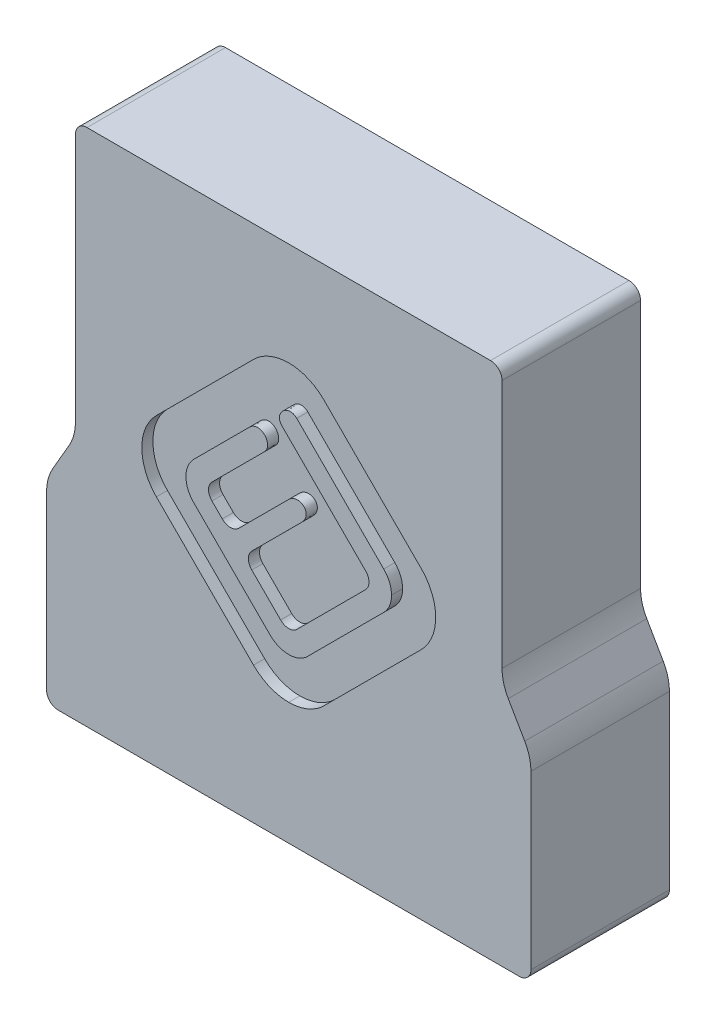
SolidWorks part; units mm, degrees
material "Mahogany"
ref_plane "Front Plane" through (0, 0, 0) normal (0, 0, 1) x (1, 0, 0)
ref_plane "Top Plane" through (0, 0, 0) normal (0, 1, 0) x (1, 0, 0)
ref_plane "Right Plane" through (0, 0, 0) normal (1, 0, 0) x (0, 0, -1)
sketch "Sketch1" plane through (0, 0, 0) normal (0, 0, 1) x (1, 0, 0)
  line L0 (-17.4943, -33.274) -> (17.4943, -33.274)
  line L1 (17.4943, -33.274) -> (17.4943, -38.862)
  line L2 (17.4943, -38.862) -> (30.1308, -38.862)
  line L3 (30.1308, -38.862) -> (30.1308, -18.288)
  line L4 (30.1308, -18.288) -> (26.162, -18.288)
  line L5 (26.162, 26.162) -> (-26.162, 26.162)
  line L6 (0, 0) -> (0, -33.274) construction
  line L7 (26.162, -18.288) -> (26.162, 26.162)
  line L15 (-26.162, -18.288) -> (-26.162, 26.162)
  line L16 (-30.1308, -18.288) -> (-26.162, -18.288)
  line L17 (-30.1308, -38.862) -> (-30.1308, -18.288)
  line L18 (-17.4943, -38.862) -> (-30.1308, -38.862)
  line L19 (-17.4943, -33.274) -> (-17.4943, -38.862)
  point P26 (0, 26.162)
  dimension "D1" = 59.436
  dimension "D2" = 34.9885
  dimension "D3" = 65.024
  dimension "D4" = 60.2615
  dimension "D5" = 20.574
  dimension "D6" = 52.324
  dimension "D7" = 26.162
extrude "Overlap Profile" add sketch "Sketch1" against normal blind 5.08 thin
sketch "Sketch2" plane through (0, 0, 0) normal (0, 0, 1) x (1, 0, 0)
  line L0 (-29.337, 29.337) -> (-29.337, -15.113) construction
  line L1 (29.337, 29.337) -> (-29.337, 29.337) construction
  line L2 (29.337, -15.113) -> (29.337, 29.337) construction
  line L3 (33.3058, -15.113) -> (29.337, -15.113) construction
  line L4 (33.3058, -42.037) -> (33.3058, -15.113) construction
  line L5 (14.3193, -42.037) -> (33.3058, -42.037) construction
  line L6 (14.3193, -36.449) -> (14.3193, -42.037) construction
  line L7 (-14.3193, -36.449) -> (14.3193, -36.449) construction
  line L8 (-14.3193, -42.037) -> (-14.3193, -36.449) construction
  line L9 (-33.3058, -42.037) -> (-14.3193, -42.037) construction
  line L10 (-33.3058, -15.113) -> (-33.3058, -42.037) construction
  line L11 (-29.337, -15.113) -> (-33.3058, -15.113) construction
  line L12 (-29.337, 29.337) -> (-29.337, -15.113)
  line L13 (29.337, 29.337) -> (-29.337, 29.337)
  line L14 (29.337, -15.113) -> (29.337, 29.337)
  line L15 (33.3058, -15.113) -> (29.337, -15.113)
  line L16 (33.3058, -42.037) -> (33.3058, -15.113)
  line L17 (14.3193, -42.037) -> (33.3058, -42.037)
  line L18 (14.3193, -36.449) -> (14.3193, -42.037)
  line L19 (-14.3193, -36.449) -> (14.3193, -36.449)
  line L20 (-14.3193, -42.037) -> (-14.3193, -36.449)
  line L21 (-33.3058, -42.037) -> (-14.3193, -42.037)
  line L22 (-33.3058, -15.113) -> (-33.3058, -42.037)
  line L23 (-29.337, -15.113) -> (-33.3058, -15.113)
extrude "End Thickness" add sketch "Sketch2" along normal blind 13.97
fillet "Fillet1" radius 1.5875 12 edges at (-26.162, 26.162, -2.54) (-26.162, -18.288, -2.54) (-30.1308, -18.288, -2.54) (-30.1308, -38.862, -2.54) (17.4943, -33.274, -2.54) (17.4943, -38.862, -2.54) (30.1308, -38.862, -2.54) (30.1308, -18.288, -2.54) (26.162, -18.288, -2.54) (26.162, 26.162, -2.54) (-17.4943, -33.274, -2.54) (-17.4943, -38.862, -2.54)
fillet "Fillet2" radius 1.5875 4 edges at (-29.337, 29.337, 4.445) (29.337, 29.337, 4.445) (33.3058, -42.037, 4.445) (-33.3058, -42.037, 4.445)
sketch "Sketch7" plane through (0, 0, -5.08) normal (0, 0, -1) x (-1, 0, 0)
  line L1 (-14.3193, -36.449) -> (14.3193, -36.449)
  line L2 (-14.3193, -36.449) -> (-14.3193, -42.037)
  line L3 (-14.3193, -42.037) -> (14.3193, -42.037)
  line L4 (14.3193, -36.449) -> (14.3193, -42.037)
extrude "Bottom Fill" add sketch "Sketch7" against normal up to surface (19.05 mm away) up to face at (0, -16.764, 13.97)
sketch "Sketch5" plane through (0, 0, 13.97) normal (0, 0, 1) x (1, 0, 0)
  line L0 (13.0646, -8.006) -> (2.5845, -18.4871)
  line L1 (-2.5844, -18.4855) -> (-13.0646, -8.006)
  line L2 (-11.085, -6.0269) -> (-8.0174, -9.0969)
  line L3 (-6.2094, -10.9033) -> (-0.6055, -16.5074)
  line L4 (0.606, -16.5078) -> (11.0865, -6.0272)
  line L5 (18.2052, -0.1879) -> (4.8438, 13.1736)
  line L6 (-4.8432, 13.1736) -> (-18.2053, -0.1879)
  line L7 (-18.2049, -9.8749) -> (-4.8432, -23.2365)
  line L8 (4.8438, -23.2365) -> (18.2052, -9.8749)
  line L9 (0, 13.9458) -> (0, 70.9204) construction
  spline S0 degree 3 poles (2.5845, -18.4871) (1.8952, -19.1776) (0.9773, -19.5586) (0, -19.5575) knots 1 1 1 1 2 2 2 2
  spline S1 degree 3 poles (0, -19.5575) (-0.9767, -19.5575) (-1.8933, -19.1776) (-2.5844, -18.4855) knots 2 2 2 2 3 3 3 3
  spline S2 degree 3 poles (-13.0646, -8.006) (-13.756, -7.316) (-14.136, -6.3986) (-14.136, -5.4217) knots 4 4 4 4 5 5 5 5
  spline S3 degree 3 poles (-14.136, -5.4217) (-14.136, -4.4447) (-13.7556, -3.5278) (-13.0646, -2.8373) knots 5 5 5 5 6 6 6 6
  spline S4 degree 2 poles (-13.0646, -2.8373) (-8.1998, 2.0277) (-5.4287, 4.7988) knots 6 6 6 7 7 7
  spline S5 degree 3 poles (-5.4287, 4.7988) (-3.8393, 6.3872) (-2.073, 4.196) (-3.3333, 2.9364) knots 7 7 7 7 8 8 8 8
  spline S6 degree 2 poles (-3.3333, 2.9364) (-6.1042, 0.1638) (-11.0861, -4.8163) knots 8 8 8 9 9 9
  spline S7 degree 3 poles (-11.0861, -4.8163) (-11.2473, -4.9784) (-11.3367, -5.1929) (-11.3367, -5.4217) knots 9 9 9 9 10 10 10 10
  spline S8 degree 3 poles (-11.3367, -5.4217) (-11.3361, -5.6501) (-11.2473, -5.8652) (-11.085, -6.0269) knots 10 10 10 10 11 11 11 11
  spline S9 degree 2 poles (-8.0174, -9.0969) (-1.828, -2.9089) (-0.0253, -1.1061) knots 12 12 12 13 13 13
  spline S10 degree 3 poles (-0.0253, -1.1061) (1.429, 0.3476) (3.4298, -1.2637) (1.8008, -2.8935) knots 13 13 13 13 14 14 14 14
  spline S11 degree 2 poles (1.8008, -2.8935) (0.0954, -4.5994) (-6.2094, -10.9033) knots 14 14 14 15 15 15
  spline S12 degree 3 poles (-0.6055, -16.5074) (-0.4437, -16.6691) (-0.2284, -16.7584) (0, -16.7584) knots 16 16 16 16 17 17 17 17
  spline S13 degree 3 poles (0, -16.7584) (0.2296, -16.7584) (0.4438, -16.6698) (0.606, -16.5078) knots 17 17 17 17 18 18 18 18
  spline S14 degree 3 poles (11.0865, -6.0272) (11.2476, -5.8652) (11.3364, -5.6494) (11.3368, -5.4226) knots 19 19 19 19 20 20 20 20
  spline S15 degree 3 poles (11.3368, -5.4226) (11.3368, -5.1929) (11.2476, -4.9777) (11.0858, -4.8163) knots 20 20 20 20 21 21 21 21
  spline S16 degree 2 poles (11.0858, -4.8163) (2.5929, 3.6758) (-0.914, 7.1841) knots 21 21 21 22 22 22
  spline S17 degree 3 poles (-0.914, 7.1841) (-2.1169, 8.3858) (-0.0785, 10.3075) (1.1034, 9.1246) knots 22 22 22 22 23 23 23 23
  spline S18 degree 2 poles (1.1034, 9.1246) (4.6697, 5.5578) (13.0646, -2.8373) knots 23 23 23 24 24 24
  spline S19 degree 3 poles (13.0646, -2.8373) (13.7564, -3.5274) (14.1361, -4.4447) (14.1361, -5.4213) knots 24 24 24 24 25 25 25 25
  spline S20 degree 3 poles (14.1361, -5.4213) (14.1361, -6.3974) (13.7564, -7.316) (13.0646, -8.006) knots 25 25 25 25 26 26 26 26
  spline S21 degree 3 poles (4.8438, 13.1736) (3.5495, 14.4676) (1.8293, 15.1801) (0, 15.1801) knots 1 1 1 1 2 2 2 2
  spline S22 degree 3 poles (0, 15.1801) (-1.8295, 15.1801) (-3.5499, 14.4676) (-4.8432, 13.1736) knots 2 2 2 2 3 3 3 3
  spline S23 degree 3 poles (-18.2053, -0.1879) (-20.8754, -2.8587) (-20.8754, -7.204) (-18.2049, -9.8749) knots 4 4 4 4 5 5 5 5
  spline S24 degree 3 poles (-4.8432, -23.2365) (-3.5499, -24.5303) (-1.8295, -25.2429) (0, -25.2429) knots 6 6 6 6 7 7 7 7
  spline S25 degree 3 poles (0, -25.2429) (1.8293, -25.2429) (3.5495, -24.5303) (4.8438, -23.2365) knots 7 7 7 7 8 8 8 8
  spline S26 degree 3 poles (18.2052, -9.8749) (20.8765, -7.204) (20.8765, -2.8587) (18.2052, -0.1879) knots 9 9 9 9 10 10 10 10
extrude "Logo Inlay Cutout" cut sketch "Sketch5" against normal blind 1.524
sketch "Sketch9" plane through (0, 0, 13.97) normal (0, 0, 1) x (1, 0, 0)
  line L0 (-33.3058, -15.113) -> (-29.337, -8.2389)
  line L1 (-29.337, 27.7495) -> (-29.337, -15.113) construction
  line L2 (-29.337, -8.2389) -> (-29.337, -15.113)
  line L3 (-29.337, -15.113) -> (-33.3058, -15.113)
  line L4 (0, 0) -> (0, -49.9352) construction
  line L5 (29.337, -15.113) -> (33.3058, -15.113)
  line L6 (29.337, -8.2389) -> (29.337, -15.113)
  line L7 (33.3058, -15.113) -> (29.337, -8.2389)
  dimension "D1" = 60
extrude "Side Transition Fill" add sketch "Sketch9" against normal up to surface (19.05 mm away)
sketch "Sketch8" plane through (0, 0, 0) normal (0, 0, -1) x (-1, 0, 0)
  line L0 (-26.162, -16.7005) -> (-26.162, 24.5745) construction
  line L1 (-26.162, -2.0955) -> (26.162, -2.0955)
  line L2 (-26.162, -2.0955) -> (-26.162, -22.9235)
  line L3 (-26.162, -22.9235) -> (26.162, -22.9235)
  line L4 (26.162, -2.0955) -> (26.162, -22.9235)
  line L5 (26.162, 24.5745) -> (26.162, -16.7005) construction
  line L8 (31.7183, -42.037) -> (-31.7183, -42.037) construction
  dimension "D1" = 19.1135
  dimension "D2" = 39.9415
extrude "Magnetic Catch Cutout" cut sketch "Sketch8" against normal blind 7.62
fillet "Fillet3" radius 6.35 2 edges at (29.337, -8.2389, 4.445) (-29.337, -8.2389, 4.445)
fillet "Fillet4" radius 6.35 2 edges at (33.3058, -15.113, 4.445) (-33.3058, -15.113, 4.445)
sketch "Sketch10" plane through (0, 0, 0) normal (0, 0, -1) x (-1, 0, 0)
  line L0 (26.162, -2.0955) -> (-26.162, -2.0955) construction
  line L1 (-26.162, -22.9235) -> (26.162, -22.9235) construction
  line L2 (-26.162, -16.7005) -> (-26.162, 24.5745) construction
  line L3 (-26.162, -2.0955) -> (-26.162, -22.9235) construction
  line L4 (26.162, -22.9235) -> (26.162, -16.7005) construction
  line L5 (26.162, 24.5745) -> (26.162, -2.0955) construction
  circle A0 centre (-22.987, -2.0955) radius 3.175
  circle A1 centre (-22.987, -22.9235) radius 3.175
  circle A2 centre (22.987, -22.9235) radius 3.175
  circle A3 centre (22.987, -2.0955) radius 3.175
  dimension "D1" = 6.35
extrude "Router Bit Relief" cut sketch "Sketch10" against normal up to surface (7.62 mm away) up to face at (0, -12.5095, 7.62)
fillet "Fillet5" radius 3.175 4 edges at (-19.812, -2.0955, 3.81) (-19.812, -22.9235, 3.81) (19.812, -22.9235, 3.81) (19.812, -2.0955, 3.81)
sketch "Sketch15" plane through (0, 0, 13.97) normal (0, 0, 1) x (1, 0, 0)
  line L0 (-8.0174, -9.0969) -> (-11.085, -6.0269) construction
  line L1 (-8.0174, -9.0969) -> (-11.085, -6.0269) construction
  line L2 (-0.6055, -16.5074) -> (-6.2094, -10.9033) construction
  line L3 (11.0865, -6.0272) -> (0.606, -16.5078) construction
  line L4 (11.0865, -6.0272) -> (0.606, -16.5078) construction
  line L5 (1.123, -15.9908) -> (0.606, -16.5078)
  line L6 (-5.0869, -12.0259) -> (-6.2094, -10.9033)
  line L7 (-10.5689, -6.5434) -> (-11.085, -6.0269)
  line L18 (2.5845, -18.4871) -> (13.0646, -8.006)
  line L19 (11.0865, -6.0272) -> (0.606, -16.5078)
  line L20 (-0.6055, -16.5074) -> (-6.2094, -10.9033)
  line L21 (-8.0174, -9.0969) -> (-11.085, -6.0269)
  line L22 (-13.0646, -8.006) -> (-2.5844, -18.4855)
  line L24 (11.0865, -6.0272) -> (10.569, -6.5446)
  line L25 (-0.6055, -16.5074) -> (-1.1221, -15.9908)
  line L26 (-8.0174, -9.0969) -> (-9.1398, -7.9736)
  arc A0 (-10.5682, -4.2986) -> (-10.5689, -6.5434) centre (-9.4459, -5.4213) ccw
  arc A1 (-9.1398, -7.9736) -> (-6.8944, -7.9742) centre (-8.0168, -6.8515) ccw
  arc A2 (-5.0868, -9.7808) -> (-5.0869, -12.0259) centre (-3.9643, -10.9034) ccw
  arc A3 (-1.1221, -15.9908) -> (1.123, -15.9908) centre (0.0004, -14.8683) ccw
  arc A4 (10.569, -6.5446) -> (10.569, -4.2995) centre (9.4465, -5.4221) ccw
  spline S0 degree 2 poles (-11.0861, -4.8163) (-6.1042, 0.1638) (-3.3333, 2.9364) knots 8 8 8 9 9 9 construction
  spline S2 degree 2 poles (-0.0253, -1.1061) (-1.828, -2.9089) (-8.0174, -9.0969) knots 12 12 12 13 13 13 construction
  spline S3 degree 2 poles (-6.2094, -10.9033) (0.0954, -4.5994) (1.8008, -2.8935) knots 14 14 14 15 15 15 construction
  spline S4 degree 2 poles (-0.914, 7.1841) (2.5929, 3.6758) (11.0858, -4.8163) knots 21 21 21 22 22 22 construction
  spline S38 degree 3 poles (39.3725, 991.6475) (-248.9242, -982.5134) (490.0971, 884.4746) (-651.7572, -751.4605) knots 8.019112 8.019112 8.019112 8.019112 43.041313 43.041313 43.041313 43.041313 only from (13.0646, -8.006) to (14.1361, -5.4213)
  spline S39 degree 3 poles (-658.7252, 734.3466) (496.1293, -891.1219) (-253.4308, 969.6155) (41.6749, -1002.414) knots 6.887684 6.887684 6.887684 6.887684 42.07325 42.07325 42.07325 42.07325 only from (14.1361, -5.4213) to (13.0646, -2.8373)
  spline S40 degree 2 poles (720.1797, -709.9348) (-717.2395, 727.4377) (708.2263, -697.9529) knots 12.5129 12.5129 12.5129 36.862628 36.862628 36.862628 only from (13.0646, -2.8373) to (1.1034, 9.1246)
  spline S41 degree 3 poles (-611.0838, -781.5838) (706.3628, 742.4374) (-781.2676, -645.7301) (829.654, 564.0856) knots 16.842586 16.842586 16.842586 16.842586 28.136888 28.136888 28.136888 28.136888 only from (1.1034, 9.1246) to (-0.914, 7.1841)
  spline S42 degree 2 poles (2120.8758, -2113.5966) (-2133.5368, 2138.9167) (2132.6918, -2125.6396) knots -0.344255 -0.344255 -0.344255 40.994874 40.994874 40.994874 only from (-0.914, 7.1841) to (11.0858, -4.8163)
  spline S43 degree 3 poles (749.7299, -2908.8051) (-1016.2633, 2816.4948) (1313.8777, -2710.6912) (-1552.3955, 2550.6403) knots -20.721468 -20.721468 -20.721468 -20.721468 61.722928 61.722928 61.722928 61.722928 only from (11.0858, -4.8163) to (11.3368, -5.4226)
  spline S44 degree 3 poles (-1427.7352, -2634.0556) (1198.8921, 2755.3096) (-912.4021, -2865.8999) (658.5281, 2920.0551) knots -20.883865 -20.883865 -20.883865 -20.883865 59.79428 59.79428 59.79428 59.79428 only from (11.3368, -5.4226) to (11.0865, -6.0272)
  spline S45 degree 3 poles (-2912.0245, -719.0392) (2827.1464, 989.0057) (-2706.3149, -1311.3968) (2552.1599, 1552.6637) knots -24.742629 -24.742629 -24.742629 -24.742629 59.741029 59.741029 59.741029 59.741029 only from (0.606, -16.5078) to (0, -16.7584)
  spline S46 degree 3 poles (-2566.651, 1529.8627) (2711.8644, -1308.3233) (-2825.0037, 1005.8401) (2903.3943, -755.939) knots -24.336799 -24.336799 -24.336799 -24.336799 57.358319 57.358319 57.358319 57.358319 only from (0, -16.7584) to (-0.6055, -16.5074)
  spline S47 degree 2 poles (-2127.7761, -2131.8916) (2128.631, 2123.3195) (-2119.761, -2123.7978) knots -6.150124 -6.150124 -6.150124 36.851174 36.851174 36.851174 only from (-6.2094, -10.9033) to (1.8008, -2.8935)
  spline S48 degree 3 poles (-912.4395, 402.2691) (857.2638, -534.4785) (-768.436, 649.0923) (660.6969, -751.7121) knots 7.784488 7.784488 7.784488 7.784488 19.343438 19.343438 19.343438 19.343438 only from (1.8008, -2.8935) to (-0.0253, -1.1061)
  spline S49 degree 2 poles (-2121.7285, -2122.0307) (2127.0994, 2125.2715) (-2129.6154, -2129.9796) knots -10.407218 -10.407218 -10.407218 33.626154 33.626154 33.626154 only from (-0.0253, -1.1061) to (-8.0174, -9.0969)
  spline S50 degree 3 poles (-604.873, 2931.0468) (873.0827, -2875.7574) (-1174.7296, 2762.9648) (1419.4807, -2638.2337) knots -30.649604 -30.649604 -30.649604 -30.649604 51.821766 51.821766 51.821766 51.821766 only from (-11.085, -6.0269) to (-11.3367, -5.4217)
  spline S51 degree 3 poles (1652.0366, 2487.0149) (-1419.3533, -2657.1876) (1125.0895, 2774.2857) (-859.2116, -2878.6067) knots -31.901781 -31.901781 -31.901781 -31.901781 51.089545 51.089545 51.089545 51.089545 only from (-11.3367, -5.4217) to (-11.0861, -4.8163)
  spline S52 degree 2 poles (-2133.9266, -2124.5614) (2130.5056, 2133.3187) (-2126.5341, -2116.4085) knots -20.814083 -20.814083 -20.814083 41.26662 41.26662 41.26662 only from (-11.0861, -4.8163) to (-3.3333, 2.9364)
  spline S53 degree 3 poles (-709.6892, 710.7921) (617.6693, -797.9234) (-521.0716, 877.4505) (394.7657, -911.6253) knots 1.825931 1.825931 1.825931 1.825931 13.04255 13.04255 13.04255 13.04255 only from (-3.3333, 2.9364) to (-5.4287, 4.7988)
  spline S54 degree 2 poles (-712.4869, -702.3557) (712.7781, 723.0868) (-720.1332, -709.9744) knots -13.74806 -13.74806 -13.74806 23.199766 23.199766 23.199766 only from (-5.4287, 4.7988) to (-13.0646, -2.8373)
  spline S55 degree 3 poles (-55.5356, -1001.935) (267.8313, 965.516) (-509.471, -883.6085) (669.6657, 724.242) knots -12.123798 -12.123798 -12.123798 -12.123798 23.104141 23.104141 23.104141 23.104141 only from (-13.0646, -2.8373) to (-14.136, -5.4217)
  spline S56 degree 3 poles (661.9446, -742.2491) (-500.374, 878.0489) (258.324, -979.2181) (-46.7656, 991.4148) knots -13.097646 -13.097646 -13.097646 -13.097646 22.075826 22.075826 22.075826 22.075826 only from (-14.136, -5.4217) to (-13.0646, -8.006)
  spline S57 degree 3 poles (996.9408, -49.2898) (-973.0774, 252.4311) (881.7023, -507.3258) (-733.8975, 659.6797) knots -15.164973 -15.164973 -15.164973 -15.164973 20.175647 20.175647 20.175647 20.175647 only from (-2.5844, -18.4855) to (0, -19.5575)
  spline S58 degree 3 poles (727.4798, 666.5714) (-875.8778, -520.687) (969.2511, 271.319) (-995.9408, -72.5264) knots -15.979909 -15.979909 -15.979909 -15.979909 19.023533 19.023533 19.023533 19.023533 only from (0, -19.5575) to (2.5845, -18.4871)
  spline S63 degree 2 poles (10.569, -4.2995) (10.825, -4.5556) (11.0858, -4.8163) knots 21.969298 21.969298 21.969298 22 22 22
  spline S64 degree 3 poles (11.0858, -4.8163) (11.2476, -4.9777) (11.3368, -5.1929) (11.3368, -5.4226) knots 20 20 20 20 21 21 21 21
  spline S65 degree 3 poles (11.3368, -5.4226) (11.3364, -5.6494) (11.2476, -5.8652) (11.0865, -6.0272) knots 19 19 19 19 20 20 20 20
  spline S66 degree 3 poles (0.606, -16.5078) (0.4438, -16.6698) (0.2296, -16.7584) (0, -16.7584) knots 17 17 17 17 18 18 18 18
  spline S67 degree 3 poles (0, -16.7584) (-0.2284, -16.7584) (-0.4437, -16.6691) (-0.6055, -16.5074) knots 16 16 16 16 17 17 17 17
  spline S68 degree 2 poles (-6.2094, -10.9033) (-5.6286, -10.3225) (-5.0868, -9.7808) knots 14 14 14 14.092128 14.092128 14.092128
  spline S70 degree 2 poles (-6.8944, -7.9742) (-7.4366, -8.5162) (-8.0174, -9.0969) knots 12.906163 12.906163 12.906163 13 13 13
  spline S71 degree 3 poles (-11.085, -6.0269) (-11.2473, -5.8652) (-11.3361, -5.6501) (-11.3367, -5.4217) knots 10 10 10 10 11 11 11 11
  spline S72 degree 3 poles (-11.3367, -5.4217) (-11.3367, -5.1929) (-11.2473, -4.9784) (-11.0861, -4.8163) knots 9 9 9 9 10 10 10 10
  spline S73 degree 2 poles (-11.0861, -4.8163) (-10.8241, -4.5544) (-10.5682, -4.2986) knots 8 8 8 8.052589 8.052589 8.052589
  dimension "D1" = 1.5875
  dimension "D3" = 0
extrude "Logo Fill for 1/8\" Router Bit" add sketch "Sketch15" against normal up to surface (1.524 mm away) up to face at (-0.7738, -6.624, 12.446)
sketch "Toolpath Sketch 1" plane through (0, 0, 0) normal (0, 0, 1) x (1, 0, 0)
  line L0 (30.1308, -37.2745) -> (30.1308, -19.8755) construction
  line L1 (28.5433, -18.288) -> (27.7495, -18.288) construction
  line L2 (26.162, -16.7005) -> (26.162, 24.5745) construction
  line L3 (24.5745, 26.162) -> (-24.5745, 26.162) construction
  line L4 (19.0818, -38.862) -> (28.5433, -38.862) construction
  line L5 (17.4943, -34.8615) -> (17.4943, -37.2745) construction
  line L6 (-15.9068, -33.274) -> (15.9068, -33.274) construction
  line L7 (-17.4943, -37.2745) -> (-17.4943, -34.8615) construction
  line L8 (-28.5433, -38.862) -> (-19.0818, -38.862) construction
  line L9 (-30.1308, -19.8755) -> (-30.1308, -37.2745) construction
  line L10 (-27.7495, -18.288) -> (-28.5433, -18.288) construction
  line L11 (-26.162, 24.5745) -> (-26.162, -16.7005) construction
  line L12 (30.1308, -37.2745) -> (30.1308, -19.8755)
  line L13 (28.5433, -18.288) -> (27.7495, -18.288)
  line L14 (26.162, -16.7005) -> (26.162, 24.5745)
  line L15 (24.5745, 26.162) -> (-24.5745, 26.162)
  line L16 (19.0818, -38.862) -> (28.5433, -38.862)
  line L17 (17.4943, -34.8615) -> (17.4943, -37.2745)
  line L18 (-15.9068, -33.274) -> (15.9068, -33.274)
  line L19 (-17.4943, -37.2745) -> (-17.4943, -34.8615)
  line L20 (-28.5433, -38.862) -> (-19.0818, -38.862)
  line L21 (-30.1308, -19.8755) -> (-30.1308, -37.2745)
  line L22 (-27.7495, -18.288) -> (-28.5433, -18.288)
  line L23 (-26.162, 24.5745) -> (-26.162, -16.7005)
  line L25 (-18.415, 22.987) -> (18.415, 22.987)
  line L26 (-22.987, 18.415) -> (-22.987, -25.527)
  line L27 (-18.415, -30.099) -> (18.415, -30.099)
  line L28 (22.987, 18.415) -> (22.987, -25.527)
  line L29 (-24.511, 24.5745) -> (24.5745, 24.5745)
  line L30 (-24.511, 24.5745) -> (-24.511, -31.623)
  line L31 (-24.511, -31.623) -> (24.5745, -31.623)
  line L32 (24.5745, 24.5745) -> (24.5745, -31.623)
  arc A0 (30.1308, -19.8755) -> (28.5433, -18.288) centre (28.5433, -19.8755) ccw construction
  arc A1 (26.162, -16.7005) -> (27.7495, -18.288) centre (27.7495, -16.7005) ccw construction
  arc A2 (26.162, 24.5745) -> (24.5745, 26.162) centre (24.5745, 24.5745) ccw construction
  arc A3 (-24.5745, 26.162) -> (-26.162, 24.5745) centre (-24.5745, 24.5745) ccw construction
  arc A4 (28.5433, -38.862) -> (30.1308, -37.2745) centre (28.5433, -37.2745) ccw construction
  arc A5 (17.4943, -37.2745) -> (19.0818, -38.862) centre (19.0818, -37.2745) ccw construction
  arc A6 (17.4943, -34.8615) -> (15.9068, -33.274) centre (15.9068, -34.8615) ccw construction
  arc A7 (-15.9068, -33.274) -> (-17.4943, -34.8615) centre (-15.9068, -34.8615) ccw construction
  arc A8 (-19.0818, -38.862) -> (-17.4943, -37.2745) centre (-19.0818, -37.2745) ccw construction
  arc A9 (-30.1308, -37.2745) -> (-28.5433, -38.862) centre (-28.5433, -37.2745) ccw construction
  arc A10 (-28.5433, -18.288) -> (-30.1308, -19.8755) centre (-28.5433, -19.8755) ccw construction
  arc A11 (-27.7495, -18.288) -> (-26.162, -16.7005) centre (-27.7495, -16.7005) ccw construction
  arc A12 (30.1308, -19.8755) -> (28.5433, -18.288) centre (28.5433, -19.8755) ccw
  arc A13 (26.162, -16.7005) -> (27.7495, -18.288) centre (27.7495, -16.7005) ccw
  arc A14 (26.162, 24.5745) -> (24.5745, 26.162) centre (24.5745, 24.5745) ccw
  arc A15 (-24.5745, 26.162) -> (-26.162, 24.5745) centre (-24.5745, 24.5745) ccw
  arc A16 (28.5433, -38.862) -> (30.1308, -37.2745) centre (28.5433, -37.2745) ccw
  arc A17 (17.4943, -37.2745) -> (19.0818, -38.862) centre (19.0818, -37.2745) ccw
  arc A18 (17.4943, -34.8615) -> (15.9068, -33.274) centre (15.9068, -34.8615) ccw
  arc A19 (-15.9068, -33.274) -> (-17.4943, -34.8615) centre (-15.9068, -34.8615) ccw
  arc A20 (-19.0818, -38.862) -> (-17.4943, -37.2745) centre (-19.0818, -37.2745) ccw
  arc A21 (-30.1308, -37.2745) -> (-28.5433, -38.862) centre (-28.5433, -37.2745) ccw
  arc A22 (-28.5433, -18.288) -> (-30.1308, -19.8755) centre (-28.5433, -19.8755) ccw
  arc A23 (-27.7495, -18.288) -> (-26.162, -16.7005) centre (-27.7495, -16.7005) ccw
  arc A24 (-22.987, -25.527) -> (-18.415, -30.099) centre (-18.415, -25.527) ccw
  arc A25 (18.415, -30.099) -> (22.987, -25.527) centre (18.415, -25.527) ccw
  arc A26 (18.415, 22.987) -> (22.987, 18.415) centre (18.415, 18.415) cw
  arc A27 (-18.415, 22.987) -> (-22.987, 18.415) centre (-18.415, 18.415) ccw
  dimension "D5" = 4.572
  dimension "D1" = 3.175
  dimension "D2" = 3.175
  dimension "D3" = 3.175
  dimension "D4" = 3.175
  dimension "D6" = 1.524
  dimension "D7" = 1.524
sketch "Toolpath Sketch 2" plane through (0, 0, 0) normal (0, 0, 1) x (1, 0, 0)
  line L4 (-26.162, -2.0955) -> (-26.162, -22.9235)
  line L5 (17.4877, -2.0955) -> (-17.4877, -2.0955)
  line L6 (26.162, -22.9235) -> (26.162, -2.0955)
  line L7 (-17.4877, -22.9235) -> (17.4877, -22.9235)
  line L8 (-26.162, -2.0955) -> (-26.162, -22.9235)
  line L9 (17.4877, -2.0955) -> (-17.4877, -2.0955)
  line L10 (26.162, -22.9235) -> (26.162, -2.0955)
  line L11 (-17.4877, -22.9235) -> (17.4877, -22.9235)
  arc A8 (-20.2374, -0.508) -> (-26.162, -2.0955) centre (-22.987, -2.0955) ccw
  arc A9 (-20.2374, -0.508) -> (-17.4877, -2.0955) centre (-17.4877, 1.0795) ccw
  arc A10 (17.4877, -2.0955) -> (20.2374, -0.508) centre (17.4877, 1.0795) ccw
  arc A11 (26.162, -2.0955) -> (20.2374, -0.508) centre (22.987, -2.0955) ccw
  arc A12 (20.2374, -24.511) -> (26.162, -22.9235) centre (22.987, -22.9235) ccw
  arc A13 (20.2374, -24.511) -> (17.4877, -22.9235) centre (17.4877, -26.0985) ccw
  arc A14 (-17.4877, -22.9235) -> (-20.2374, -24.511) centre (-17.4877, -26.0985) ccw
  arc A15 (-26.162, -22.9235) -> (-20.2374, -24.511) centre (-22.987, -22.9235) ccw
  arc A16 (-20.2374, -0.508) -> (-26.162, -2.0955) centre (-22.987, -2.0955) ccw
  arc A17 (-20.2374, -0.508) -> (-17.4877, -2.0955) centre (-17.4877, 1.0795) ccw
  arc A18 (17.4877, -2.0955) -> (20.2374, -0.508) centre (17.4877, 1.0795) ccw
  arc A19 (26.162, -2.0955) -> (20.2374, -0.508) centre (22.987, -2.0955) ccw
  arc A20 (20.2374, -24.511) -> (26.162, -22.9235) centre (22.987, -22.9235) ccw
  arc A21 (20.2374, -24.511) -> (17.4877, -22.9235) centre (17.4877, -26.0985) ccw
  arc A22 (-17.4877, -22.9235) -> (-20.2374, -24.511) centre (-17.4877, -26.0985) ccw
  arc A23 (-26.162, -22.9235) -> (-20.2374, -24.511) centre (-22.987, -22.9235) ccw
  dimension "D1" = 0
sketch "Toolpath Sketch 3" plane through (0, 0, 0) normal (0, 0, 1) x (1, 0, 0)
  line L4 (18.2052, -0.1879) -> (4.8438, 13.1736)
  line L5 (-4.8432, 13.1736) -> (-18.2053, -0.1879)
  line L6 (-18.2049, -9.8749) -> (-4.8432, -23.2365)
  line L7 (4.8438, -23.2365) -> (18.2052, -9.8749)
  line L8 (18.2052, -0.1879) -> (4.8438, 13.1736)
  line L9 (-4.8432, 13.1736) -> (-18.2053, -0.1879)
  line L10 (-18.2049, -9.8749) -> (-4.8432, -23.2365)
  line L11 (4.8438, -23.2365) -> (18.2052, -9.8749)
  line L13 (2.5845, -18.4871) -> (13.0646, -8.006)
  line L14 (10.569, -6.5446) -> (1.123, -15.9908)
  line L15 (-1.1221, -15.9908) -> (-5.0869, -12.0259)
  line L16 (-9.1398, -7.9736) -> (-10.5689, -6.5434)
  line L17 (-13.0646, -8.006) -> (-2.5844, -18.4855)
  line L18 (2.5845, -18.4871) -> (13.0646, -8.006)
  line L19 (10.569, -6.5446) -> (1.123, -15.9908)
  line L20 (-1.1221, -15.9908) -> (-5.0869, -12.0259)
  line L21 (-9.1398, -7.9736) -> (-10.5689, -6.5434)
  line L22 (-13.0646, -8.006) -> (-2.5844, -18.4855)
  line L26 (33.3058, -40.4495) -> (33.3058, -16.8145)
  line L27 (32.455, -13.6395) -> (30.1877, -9.7124)
  line L28 (29.337, -6.5374) -> (29.337, 27.7495)
  line L29 (27.7495, 29.337) -> (-27.7495, 29.337)
  line L30 (-29.337, 27.7495) -> (-29.337, -6.5374)
  line L31 (-30.1877, -9.7124) -> (-32.455, -13.6395)
  line L32 (-33.3058, -16.8145) -> (-33.3058, -40.4495)
  line L33 (-31.7183, -42.037) -> (31.7183, -42.037)
  line L34 (33.3058, -40.4495) -> (33.3058, -16.8145)
  line L35 (32.455, -13.6395) -> (30.1877, -9.7124)
  line L36 (29.337, -6.5374) -> (29.337, 27.7495)
  line L37 (27.7495, 29.337) -> (-27.7495, 29.337)
  line L38 (-29.337, 27.7495) -> (-29.337, -6.5374)
  line L39 (-30.1877, -9.7124) -> (-32.455, -13.6395)
  line L40 (-33.3058, -16.8145) -> (-33.3058, -40.4495)
  line L41 (-31.7183, -42.037) -> (31.7183, -42.037)
  arc A5 (-10.5682, -4.2986) -> (-10.5689, -6.5434) centre (-9.4459, -5.4213) ccw
  arc A6 (-10.5682, -4.2986) -> (-10.5689, -6.5434) centre (-9.4459, -5.4213) ccw
  arc A7 (10.569, -6.5446) -> (10.569, -4.2995) centre (9.4465, -5.4221) ccw
  arc A8 (33.3058, -16.8145) -> (32.455, -13.6395) centre (26.9558, -16.8145) ccw
  arc A9 (29.337, -6.5374) -> (30.1877, -9.7124) centre (35.687, -6.5374) ccw
  arc A10 (29.337, 27.7495) -> (27.7495, 29.337) centre (27.7495, 27.7495) ccw
  arc A11 (-27.7495, 29.337) -> (-29.337, 27.7495) centre (-27.7495, 27.7495) ccw
  arc A12 (-30.1877, -9.7124) -> (-29.337, -6.5374) centre (-35.687, -6.5374) ccw
  arc A13 (-32.455, -13.6395) -> (-33.3058, -16.8145) centre (-26.9558, -16.8145) ccw
  arc A14 (-33.3058, -40.4495) -> (-31.7183, -42.037) centre (-31.7183, -40.4495) ccw
  arc A15 (31.7183, -42.037) -> (33.3058, -40.4495) centre (31.7183, -40.4495) ccw
  arc A16 (33.3058, -16.8145) -> (32.455, -13.6395) centre (26.9558, -16.8145) ccw
  arc A17 (29.337, -6.5374) -> (30.1877, -9.7124) centre (35.687, -6.5374) ccw
  arc A18 (29.337, 27.7495) -> (27.7495, 29.337) centre (27.7495, 27.7495) ccw
  arc A19 (-27.7495, 29.337) -> (-29.337, 27.7495) centre (-27.7495, 27.7495) ccw
  arc A20 (-30.1877, -9.7124) -> (-29.337, -6.5374) centre (-35.687, -6.5374) ccw
  arc A21 (-32.455, -13.6395) -> (-33.3058, -16.8145) centre (-26.9558, -16.8145) ccw
  arc A22 (-33.3058, -40.4495) -> (-31.7183, -42.037) centre (-31.7183, -40.4495) ccw
  arc A23 (31.7183, -42.037) -> (33.3058, -40.4495) centre (31.7183, -40.4495) ccw
  arc A24 (10.569, -6.5446) -> (10.569, -4.2995) centre (9.4465, -5.4221) ccw
  arc A25 (-1.1221, -15.9908) -> (1.123, -15.9908) centre (0.0004, -14.8683) ccw
  arc A26 (-1.1221, -15.9908) -> (1.123, -15.9908) centre (0.0004, -14.8683) ccw
  arc A27 (-5.0868, -9.7808) -> (-5.0869, -12.0259) centre (-3.9643, -10.9034) ccw
  arc A28 (-5.0868, -9.7808) -> (-5.0869, -12.0259) centre (-3.9643, -10.9034) ccw
  arc A29 (-9.1398, -7.9736) -> (-6.8944, -7.9742) centre (-8.0168, -6.8515) ccw
  arc A30 (-9.1398, -7.9736) -> (-6.8944, -7.9742) centre (-8.0168, -6.8515) ccw
  spline S6 degree 3 poles (-723.4007, 2886.6208) (268.0799, -3031.8679) (268.0784, 3021.8207) (-723.4051, -2896.7286) knots -0.132756 -0.132756 -0.132756 -0.132756 19.132785 19.132785 19.132785 19.132785 only from (18.2052, -9.8749) to (18.2052, -0.1879)
  spline S7 degree 3 poles (-2968.078, 288.6038) (2882.5709, -859.3372) (-2651.974, 1432.8312) (2297.3087, -1891.8061) knots -19.010873 -19.010873 -19.010873 -19.010873 22.008765 22.008765 22.008765 22.008765 only from (4.8438, 13.1736) to (0, 15.1801)
  spline S8 degree 3 poles (-2300.5198, -1888.1123) (2654.2729, 1429.2596) (-2883.84, -856.3288) (2968.3548, 286.6642) knots -17.993564 -17.993564 -17.993564 -17.993564 22.987732 22.987732 22.987732 22.987732 only from (0, 15.1801) to (-4.8432, 13.1736)
  spline S9 degree 3 poles (722.7961, -2896.8942) (-267.6239, 3021.9445) (-268.3658, -3031.9454) (723.5104, 2886.6534) knots -5.132964 -5.132964 -5.132964 -5.132964 14.132792 14.132792 14.132792 14.132792 only from (-18.2053, -0.1879) to (-18.2049, -9.8749)
  spline S10 degree 3 poles (2968.2777, -297.3454) (-2883.6883, 846.8293) (2654.0562, -1439.8022) (-2300.2582, 1878.422) knots -13.987552 -13.987552 -13.987552 -13.987552 26.992843 26.992843 26.992843 26.992843 only from (-4.8432, -23.2365) to (0, -25.2429)
  spline S11 degree 3 poles (2297.0698, 1882.1317) (-2651.8052, -1443.4028) (2882.4975, 849.8698) (-2968.1108, -299.3086) knots -13.008105 -13.008105 -13.008105 -13.008105 28.01095 28.01095 28.01095 28.01095 only from (0, -25.2429) to (4.8438, -23.2365)
  spline S12 degree 3 poles (18.2052, -9.8749) (20.8765, -7.204) (20.8765, -2.8587) (18.2052, -0.1879) knots 9 9 9 9 10 10 10 10
  spline S13 degree 3 poles (4.8438, 13.1736) (3.5495, 14.4676) (1.8293, 15.1801) (0, 15.1801) knots 1 1 1 1 2 2 2 2
  spline S14 degree 3 poles (0, 15.1801) (-1.8295, 15.1801) (-3.5499, 14.4676) (-4.8432, 13.1736) knots 2 2 2 2 3 3 3 3
  spline S15 degree 3 poles (-18.2053, -0.1879) (-20.8754, -2.8587) (-20.8754, -7.204) (-18.2049, -9.8749) knots 4 4 4 4 5 5 5 5
  spline S16 degree 3 poles (-4.8432, -23.2365) (-3.5499, -24.5303) (-1.8295, -25.2429) (0, -25.2429) knots 6 6 6 6 7 7 7 7
  spline S17 degree 3 poles (0, -25.2429) (1.8293, -25.2429) (3.5495, -24.5303) (4.8438, -23.2365) knots 7 7 7 7 8 8 8 8
  spline S33 degree 3 poles (415.2934, 2955.6477) (-867.1396, -2882.2648) (1339.9819, 2692.4632) (-1722.6851, -2440.1694) knots 0.241481 0.241481 0.241481 0.241481 50.819232 50.819232 50.819232 50.819232 only from (13.0646, -8.006) to (14.1361, -5.4213)
  spline S34 degree 3 poles (-1742.9745, 2414.5343) (1357.8027, -2692.9458) (-881.6142, 2865.5233) (425.4554, -2964.8563) knots -0.930498 -0.930498 -0.930498 -0.930498 49.891163 49.891163 49.891163 49.891163 only from (14.1361, -5.4213) to (13.0646, -2.8373)
  spline S35 degree 2 poles (2134.3733, -2124.0787) (-2131.4553, 2141.5934) (2122.4312, -2112.0869) knots 3.706478 3.706478 3.706478 45.711837 45.711837 45.711837 only from (13.0646, -2.8373) to (1.1034, 9.1246)
  spline S36 degree 3 poles (-1949.4586, -2267.5535) (2133.7367, 2153.471) (-2287.3289, -1972.4867) (2404.092, 1797.2247) knots 14.359563 14.359563 14.359563 14.359563 30.619853 30.619853 30.619853 30.619853 only from (1.1034, 9.1246) to (-0.914, 7.1841)
  spline S37 degree 2 poles (2120.8653, -2113.5861) (-2133.2988, 2138.6788) (2132.225, -2125.173) knots -0.344204 -0.344204 -0.344204 40.992612 40.992612 40.992612 only from (-0.914, 7.1841) to (10.569, -4.2995)
  spline S42 degree 2 poles (-2126.6753, -2130.7911) (2128.0867, 2122.7753) (-2119.7712, -2123.8081) knots -6.144563 -6.144563 -6.144563 36.851225 36.851225 36.851225 only from (-5.0868, -9.7808) to (1.8008, -2.8935)
  spline S43 degree 3 poles (-2653.9112, 1385.3949) (2518.7159, -1649.6115) (-2338.2096, 1889.7499) (2127.1196, -2111.4042) knots 5.228852 5.228852 5.228852 5.228852 21.900059 21.900059 21.900059 21.900059 only from (1.8008, -2.8935) to (-0.0253, -1.1061)
  spline S44 degree 2 poles (-2121.6669, -2121.9691) (2126.5098, 2124.6821) (-2128.4958, -2128.8605) knots -10.406898 -10.406898 -10.406898 33.620363 33.620363 33.620363 only from (-0.0253, -1.1061) to (-6.8944, -7.9742)
  spline S47 degree 2 poles (-2133.3612, -2123.9969) (2130.1958, 2133.0095) (-2126.4792, -2116.3537) knots -20.809968 -20.809968 -20.809968 41.266219 41.266219 41.266219 only from (-10.5682, -4.2986) to (-3.3333, 2.9364)
  spline S48 degree 3 poles (-1994.7535, 2243.099) (1799.562, -2417.2116) (-1592.2513, 2572.0396) (1347.6936, -2669.8387) knots -0.645693 -0.645693 -0.645693 -0.645693 15.513899 15.513899 15.513899 15.513899 only from (-3.3333, 2.9364) to (-5.4287, 4.7988)
  spline S49 degree 2 poles (-2126.5243, -2116.5655) (2126.846, 2137.3167) (-2134.2182, -2124.211) knots -27.180188 -27.180188 -27.180188 36.590674 36.590674 36.590674 only from (-5.4287, 4.7988) to (-13.0646, -2.8373)
  spline S50 degree 3 poles (-467.6865, -2958.6503) (923.9696, 2851.867) (-1398.0123, -2672.2774) (1779.0267, 2387.9127) knots -19.951772 -19.951772 -19.951772 -19.951772 30.931924 30.931924 30.931924 30.931924 only from (-13.0646, -2.8373) to (-14.136, -5.4217)
  spline S51 degree 3 poles (1753.9061, -2417.3759) (-1370.6638, 2675.7675) (895.8367, -2872.0658) (-440.3956, 2951.9293) knots -20.912523 -20.912523 -20.912523 -20.912523 29.890679 29.890679 29.890679 29.890679 only from (-14.136, -5.4217) to (-13.0646, -8.006)
  spline S52 degree 3 poles (2957.9587, -440.7095) (-2865.3197, 890.252) (2677.6188, -1380.2498) (-2405.9404, 1756.4094) knots -23.021305 -23.021305 -23.021305 -23.021305 28.031761 28.031761 28.031761 28.031761 only from (-2.5844, -18.4855) to (0, -19.5575)
  spline S53 degree 3 poles (2385.409, 1784.5202) (-2659.0646, -1421.5053) (2850.672, 943.2474) (-2948.5695, -503.8046) knots -23.753374 -23.753374 -23.753374 -23.753374 26.797286 26.797286 26.797286 26.797286 only from (0, -19.5575) to (2.5845, -18.4871)
  spline S54 degree 3 poles (13.0646, -8.006) (13.7564, -7.316) (14.1361, -6.3974) (14.1361, -5.4213) knots 25 25 25 25 26 26 26 26
  spline S55 degree 3 poles (14.1361, -5.4213) (14.1361, -4.4447) (13.7564, -3.5274) (13.0646, -2.8373) knots 24 24 24 24 25 25 25 25
  spline S56 degree 2 poles (13.0646, -2.8373) (4.6697, 5.5578) (1.1034, 9.1246) knots 23 23 23 24 24 24
  spline S57 degree 3 poles (1.1034, 9.1246) (-0.0785, 10.3075) (-2.1169, 8.3858) (-0.914, 7.1841) knots 22 22 22 22 23 23 23 23
  spline S58 degree 2 poles (-0.914, 7.1841) (2.4852, 3.7835) (10.569, -4.2995) knots 21 21 21 21.969298 21.969298 21.969298
  spline S63 degree 2 poles (-5.0868, -9.7808) (0.2525, -4.4422) (1.8008, -2.8935) knots 14.092128 14.092128 14.092128 15 15 15
  spline S64 degree 3 poles (1.8008, -2.8935) (3.4298, -1.2637) (1.429, 0.3476) (-0.0253, -1.1061) knots 13 13 13 13 14 14 14 14
  spline S65 degree 2 poles (-0.0253, -1.1061) (-1.6588, -2.7398) (-6.8944, -7.9742) knots 12 12 12 12.906163 12.906163 12.906163
  spline S68 degree 2 poles (-10.5682, -4.2986) (-5.9584, 0.3096) (-3.3333, 2.9364) knots 8.052589 8.052589 8.052589 9 9 9
  spline S69 degree 3 poles (-3.3333, 2.9364) (-2.073, 4.196) (-3.8393, 6.3872) (-5.4287, 4.7988) knots 7 7 7 7 8 8 8 8
  spline S70 degree 2 poles (-5.4287, 4.7988) (-8.1998, 2.0277) (-13.0646, -2.8373) knots 6 6 6 7 7 7
  spline S71 degree 3 poles (-13.0646, -2.8373) (-13.7556, -3.5278) (-14.136, -4.4447) (-14.136, -5.4217) knots 5 5 5 5 6 6 6 6
  spline S72 degree 3 poles (-14.136, -5.4217) (-14.136, -6.3986) (-13.756, -7.316) (-13.0646, -8.006) knots 4 4 4 4 5 5 5 5
  spline S73 degree 3 poles (-2.5844, -18.4855) (-1.8933, -19.1776) (-0.9767, -19.5575) (0, -19.5575) knots 2 2 2 2 3 3 3 3
  spline S74 degree 3 poles (0, -19.5575) (0.9773, -19.5586) (1.8952, -19.1776) (2.5845, -18.4871) knots 1 1 1 1 2 2 2 2
  dimension "D1" = 0
  dimension "D2" = 0
  dimension "D3" = 0
